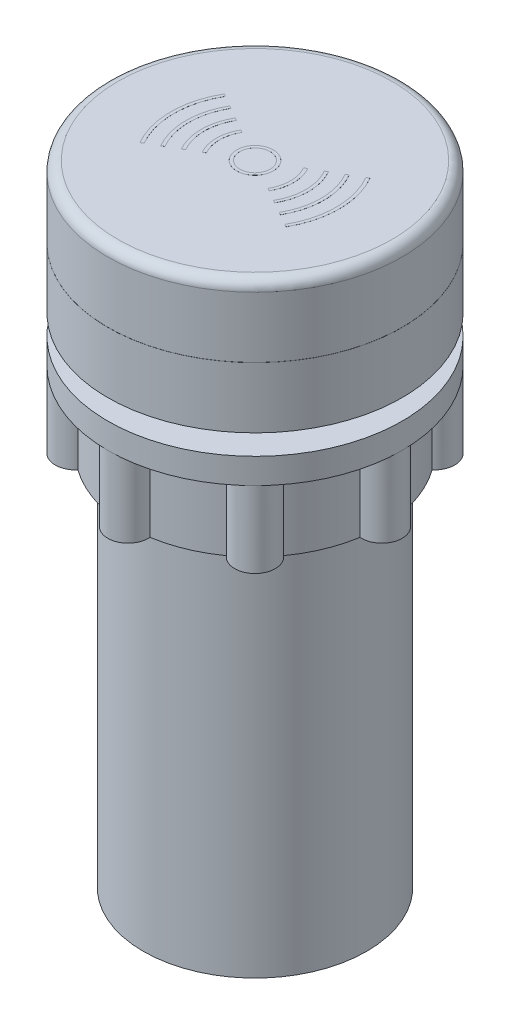
SolidWorks part; units mm, degrees
ref_plane "Front Plane" through (0, 0, 0) normal (0, 0, 1) x (1, 0, 0)
ref_plane "Top Plane" through (0, 0, 0) normal (0, 1, 0) x (1, 0, 0)
ref_plane "Right Plane" through (0, 0, 0) normal (1, 0, 0) x (0, 0, -1)
sketch "Sketch1" plane through (0, 0, 0) normal (0, 0, 1) x (1, 0, 0)
  line L0 (0, 0) -> (0, -11) construction
  line L1 (0, 0) -> (0, 62)
  line L2 (0, 62) -> (13.5, 62)
  line L4 (11, 47) -> (14.5, 47)
  line L5 (14.5, 61) -> (14.5, 55.005)
  line L6 (14.5, 47) -> (14.5, 44.5)
  line L7 (12.5, 37) -> (11, 37)
  line L8 (14.5, 49) -> (11, 49)
  line L11 (11, 49) -> (11, 47)
  line L12 (11, 0) -> (0, 0)
  line L13 (11, 37) -> (11, 0)
  line L14 (14.5, 54.995) -> (14.5, 49)
  line L15 (11, 55.005) -> (14.5, 55.005)
  line L16 (11, 55.005) -> (11, 54.995)
  line L17 (11, 54.995) -> (14.5, 54.995)
  line L19 (14.5, 44.5) -> (12.5, 44.5)
  line L20 (12.5, 44.5) -> (12.5, 37)
  arc A0 (14.5, 61) -> (13.5, 62) centre (13.5, 61) ccw
  dimension "D7" = 25
  dimension "D5" = 1
  dimension "D1" = 22
  dimension "D2" = 0.01
  dimension "D3" = 13
  dimension "D4" = 29
  dimension "D6" = 2.5
  dimension "D8" = 2
  dimension "D9" = 10
  dimension "D10" = 49
revolve "Revolve1" add sketch "Sketch1" angle 360 about L0
sketch "Sketch2" plane through (0, 44.5, 0) normal (0, -1, 0) x (1, 0, 0)
  circle A0 centre (0, 12.5) radius 2
  circle A1 centre (0, 0) radius 12.5 construction
  circle A2 centre (0, 0) radius 14.5 construction
extrude "Boss-Extrude1" add sketch "Sketch2" along normal up to surface (7.5 mm away) up to face at (-12.5, 37, 0)
pattern_circular "CirPattern1" count 8 over 360 about axis through (0, 0, 0) along (0, 1, 0) of "Boss-Extrude1"
sketch "Sketch3" plane through (0, 62, 0) normal (0, 1, 0) x (1, 0, 0)
  line L0 (-4.3301, -2.5) -> (-4.5899, -2.65)
  line L1 (-3.0311, -1.75) -> (-3.2909, -1.9)
  line L2 (0, 0) -> (-13.5, 0) construction
  line L5 (-3.0311, 1.75) -> (-3.2909, 1.9)
  line L6 (-5.6292, -3.25) -> (-5.889, -3.4)
  line L8 (-6.9282, -4) -> (-7.188, -4.15)
  line L10 (0, 0) -> (0, 1.5) construction
  line L12 (6.9282, 4) -> (7.188, 4.15)
  line L13 (-4.3301, 2.5) -> (-4.5899, 2.65)
  line L14 (5.6292, 3.25) -> (5.889, 3.4)
  line L15 (-5.6292, 3.25) -> (-5.889, 3.4)
  line L16 (4.3301, 2.5) -> (4.5899, 2.65)
  line L17 (-6.9282, 4) -> (-7.188, 4.15)
  line L18 (6.9282, -4) -> (7.188, -4.15)
  line L19 (5.6292, -3.25) -> (5.889, -3.4)
  line L20 (3.0311, 1.75) -> (3.2909, 1.9)
  line L21 (3.0311, -1.75) -> (3.2909, -1.9)
  line L22 (4.3301, -2.5) -> (4.5899, -2.65)
  circle A0 centre (0, 0) radius 1.5
  arc A2 (-4.3301, 2.5) -> (-4.3301, -2.5) centre (0, 0) ccw
  arc A3 (-5.6292, 3.25) -> (-5.6292, -3.25) centre (0, 0) ccw
  arc A4 (-6.9282, 4) -> (-6.9282, -4) centre (0, 0) ccw
  circle A6 centre (0, 0) radius 13.5 construction
  arc A7 (-3.0311, 1.75) -> (-3.0311, -1.75) centre (0, 0) ccw
  arc A8 (-3.2909, 1.9) -> (-3.2909, -1.9) centre (0, 0) ccw
  arc A9 (-4.5899, 2.65) -> (-4.5899, -2.65) centre (0, 0) ccw
  arc A10 (-5.889, 3.4) -> (-5.889, -3.4) centre (0, 0) ccw
  arc A11 (-7.188, 4.15) -> (-7.188, -4.15) centre (0, 0) ccw
  circle A12 centre (0, 0) radius 8.3 construction
  circle A13 centre (0, 0) radius 8 construction
  circle A14 centre (0, 0) radius 6.8 construction
  circle A15 centre (0, 0) radius 6.5 construction
  circle A16 centre (0, 0) radius 5.3 construction
  circle A17 centre (0, 0) radius 5 construction
  circle A18 centre (0, 0) radius 3.8 construction
  circle A19 centre (0, 0) radius 3.5 construction
  arc A20 (7.188, 4.15) -> (7.188, -4.15) centre (0, 0) cw
  arc A21 (5.889, 3.4) -> (5.889, -3.4) centre (0, 0) cw
  arc A22 (4.5899, 2.65) -> (4.5899, -2.65) centre (0, 0) cw
  arc A23 (3.2909, 1.9) -> (3.2909, -1.9) centre (0, 0) cw
  arc A24 (3.0311, 1.75) -> (3.0311, -1.75) centre (0, 0) cw
  arc A25 (6.9282, 4) -> (6.9282, -4) centre (0, 0) cw
  arc A26 (5.6292, 3.25) -> (5.6292, -3.25) centre (0, 0) cw
  arc A27 (4.3301, 2.5) -> (4.3301, -2.5) centre (0, 0) cw
  circle A28 centre (0, 0) radius 1.8
  dimension "D1" = 10
  dimension "D2" = 13
  dimension "D3" = 16
  dimension "D4" = 7
  dimension "D10" = 3
  dimension "D9" = 30
  dimension "D5" = 0.3
  dimension "D6" = 0.3
  dimension "D7" = 0.3
  dimension "D8" = 0.3
  dimension "D11" = 0.3
extrude "Boss-Extrude2" add sketch "Sketch3" along normal blind 0.005
